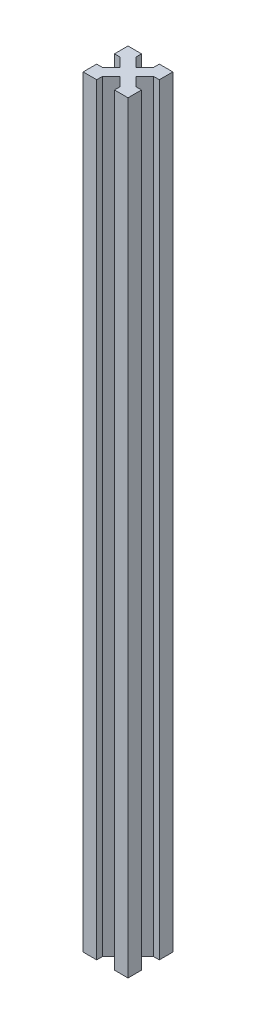
SolidWorks part; units mm, degrees
ref_plane "Plan de face" through (0, 0, 0) normal (0, 0, 1) x (1, 0, 0)
ref_plane "Plan de dessus" through (0, 0, 0) normal (0, 1, 0) x (1, 0, 0)
ref_plane "Plan de droite" through (0, 0, 0) normal (1, 0, 0) x (0, 0, -1)
sketch "Esquisse1" plane through (0, 0, 0) normal (0, 1, 0) x (1, 0, 0)
  line L0 (-2.5, 17.5) -> (-17.5, 17.5)
  line L1 (0, 0) -> (-20, 0)
  line L2 (0, 0) -> (0, 20)
  line L3 (0, 20) -> (-20, 20)
  line L4 (-20, 0) -> (-20, 20)
  line L5 (0, 20) -> (-20, 0) construction
  line L6 (-17.5, 2.5) -> (-17.5, 17.5)
  line L11 (-2.5, 2.5) -> (-17.5, 2.5)
  line L12 (-2.5, 2.5) -> (-2.5, 17.5)
  line L13 (-20, 20) -> (0, 0) construction
  line L14 (-26.9957, 23.4601) -> (-23.4601, 26.9957)
  line L15 (-26.9957, 23.4601) -> (3.4601, -6.9957)
  line L16 (-23.4601, 26.9957) -> (6.9957, -3.4601)
  line L17 (3.4601, -6.9957) -> (6.9957, -3.4601)
  line L18 (-26.9957, 23.4601) -> (6.9957, -3.4601) construction
  line L19 (-23.4601, 26.9957) -> (3.4601, -6.9957) construction
  line L20 (-10, 20) -> (-10, 0) construction
  line L21 (-23.4601, -6.9957) -> (-26.9957, -3.4601)
  line L22 (3.4601, 26.9957) -> (-26.9957, -3.4601)
  line L23 (6.9957, 23.4601) -> (-23.4601, -6.9957)
  line L24 (6.9957, 23.4601) -> (3.4601, 26.9957)
  line L25 (-17.5, 13.9645) -> (-20, 13.9645)
  line L26 (-20, 10) -> (0, 10) construction
  line L27 (-17.5, 6.0355) -> (-20, 6.0355)
  line L28 (-2.5, 6.0355) -> (0, 6.0355)
  line L29 (-2.5, 13.9645) -> (0, 13.9645)
  line L30 (-2.5, 6.0355) -> (0, 6.0355)
  line L31 (-2.5, 13.9645) -> (0, 13.9645)
  line L32 (-13.9645, 2.5) -> (-13.9645, 0)
  line L33 (-6.0355, 17.5) -> (-6.0355, 20)
  line L34 (-13.9645, 17.5) -> (-13.9645, 20)
  line L35 (-6.0355, 2.5) -> (-6.0355, 0)
  point P11 (-10, 10)
  dimension "D1" = 20
  dimension "D2" = 20
  dimension "D3" = 7.3934
  dimension "D4" = 2.5
  dimension "D5" = 43.071
  dimension "D6" = 2.5
extrude "Boss.-Extru.1" add sketch "Esquisse1" along normal blind 340 contours L15 L35 L1 | L16 L12 L11 L15 L1 L2 | L28 L16 L2 | L16 L23 L15 L11 L12 | L32 L23 L1 | L23 L11 L6 L22 L4 L1 | L22 L27 L4 | L23 L15 L22 L6 L11 | L23 L16 L22 L15 | L23 L12 L0 L22 L16 | L23 L2 L3 L22 L0 L12 | L23 L29 L2 | L33 L22 L3 | L16 L34 L3 | L16 L3 L4 L15 L6 L0 | L25 L15 L4 | L22 L16 L0 L6 L15
